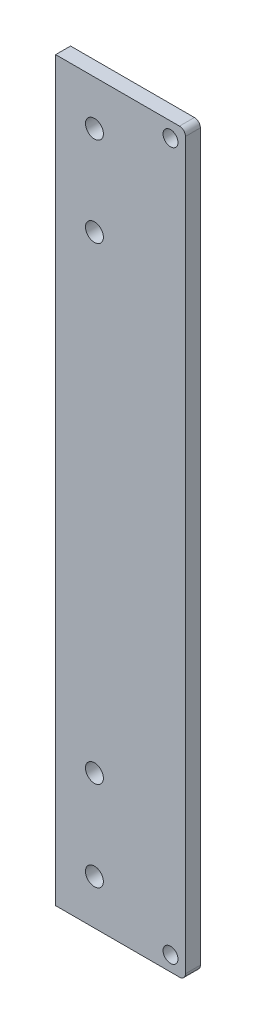
SolidWorks part; units mm, degrees
material "Glass"
ref_plane "Front Plane" through (0, 0, 0) normal (0, 0, 1) x (1, 0, 0)
ref_plane "Top Plane" through (0, 0, 0) normal (0, 1, 0) x (1, 0, 0)
ref_plane "Right Plane" through (0, 0, 0) normal (1, 0, 0) x (0, 0, -1)
sketch "Sketch1" plane through (0, 0, 0) normal (0, 0, 1) x (1, 0, 0)
  line L0 (-123.5, 121.5) -> (-123.5, -121.5)
  line L1 (-121.5, -123.5) -> (121.5, -123.5)
  line L2 (123.5, -121.5) -> (123.5, 121.5)
  line L3 (121.5, 123.5) -> (-121.5, 123.5)
  line L4 (0, 0) -> (0, 144.9076) construction
  line L5 (0, 0) -> (173.8049, 0) construction
  arc A0 (-123.5, -121.5) -> (-121.5, -123.5) centre (-121.5, -121.5) ccw
  arc A1 (121.5, -123.5) -> (123.5, -121.5) centre (121.5, -121.5) ccw
  arc A2 (123.5, 121.5) -> (121.5, 123.5) centre (121.5, 121.5) ccw
  arc A3 (-123.5, 121.5) -> (-121.5, 123.5) centre (-121.5, 121.5) cw
  circle A4 centre (-118.5, 118.5) radius 2.5
  circle A8 centre (118.5, 118.5) radius 2.5
  circle A9 centre (118.5, -118.5) radius 2.5
  circle A10 centre (-118.5, -118.5) radius 2.5
  dimension "D5" = 2
  dimension "D6" = 5
  dimension "D1" = 247
  dimension "D2" = 123.5
  dimension "D3" = 123.5
  dimension "D4" = 247
  dimension "D10" = 5
  dimension "D11" = 5
extrude "Boss-Extrude1" add sketch "Sketch1" along normal blind 5
sketch "Sketch2" plane through (0, 0, 0) normal (0, 0, -1) x (-1, 0, 0)
  line L0 (-25, 25) -> (-25, -25)
  line L1 (-25, -25) -> (25, -25)
  line L2 (25, -25) -> (25, 25)
  line L3 (25, 25) -> (-25, 25)
  line L4 (0, 0) -> (74.833, 0) construction
  line L5 (0, 0) -> (55.9239, 55.9239) construction
  line L6 (0, 0) -> (0, 65.9297) construction
  circle A0 centre (28.2843, 28.2843) radius 1.5
  circle A1 centre (28.2843, -28.2843) radius 1.5
  circle A2 centre (-28.2843, -28.2843) radius 1.5
  circle A3 centre (-28.2843, 28.2843) radius 1.5
  dimension "D7" = 3
  dimension "D1" = 25
  dimension "D2" = 25
  dimension "D3" = 25
  dimension "D4" = 25
  dimension "D5" = 45
  dimension "D6" = 40
extrude "Cut-Extrude1" cut sketch "Sketch2" against normal blind 5
sketch "Sketch3" plane through (0, 0, 0) normal (0, 0, -1) x (-1, 0, 0)
  line L0 (170, 150) -> (170, -150)
  line L1 (170, -150) -> (-80, -150)
  line L2 (-80, -150) -> (-80, 150)
  line L3 (-80, 150) -> (170, 150)
  point P2 (59.2797, 159.0273)
  point P5 (-67.7963, 151.3722)
  dimension "D1" = 80
  dimension "D2" = 250
  dimension "D3" = 150
  dimension "D4" = 300
extrude "Cut-Extrude2" cut sketch "Sketch3" against normal blind 10
sketch "Sketch4" plane through (0, 0, 0) normal (0, 0, -1) x (-1, 0, 0)
  line L0 (-80, 123.5) -> (-80, -123.5) construction
  line L1 (-121.5, 123.5) -> (-80, 123.5) construction
  line L2 (0, 0) -> (53.143, 0) construction
  circle A0 centre (-93, 78.5) radius 3
  circle A1 centre (-93, 108.5) radius 3
  circle A2 centre (-93, -78.5) radius 3
  circle A3 centre (-93, -108.5) radius 3
  dimension "D3" = 6
  dimension "D4" = 6
  dimension "D1" = 13
  dimension "D2" = 45
  dimension "D5" = 30
  dimension "D6" = 13
extrude "Cut-Extrude3" cut sketch "Sketch4" against normal blind 10
